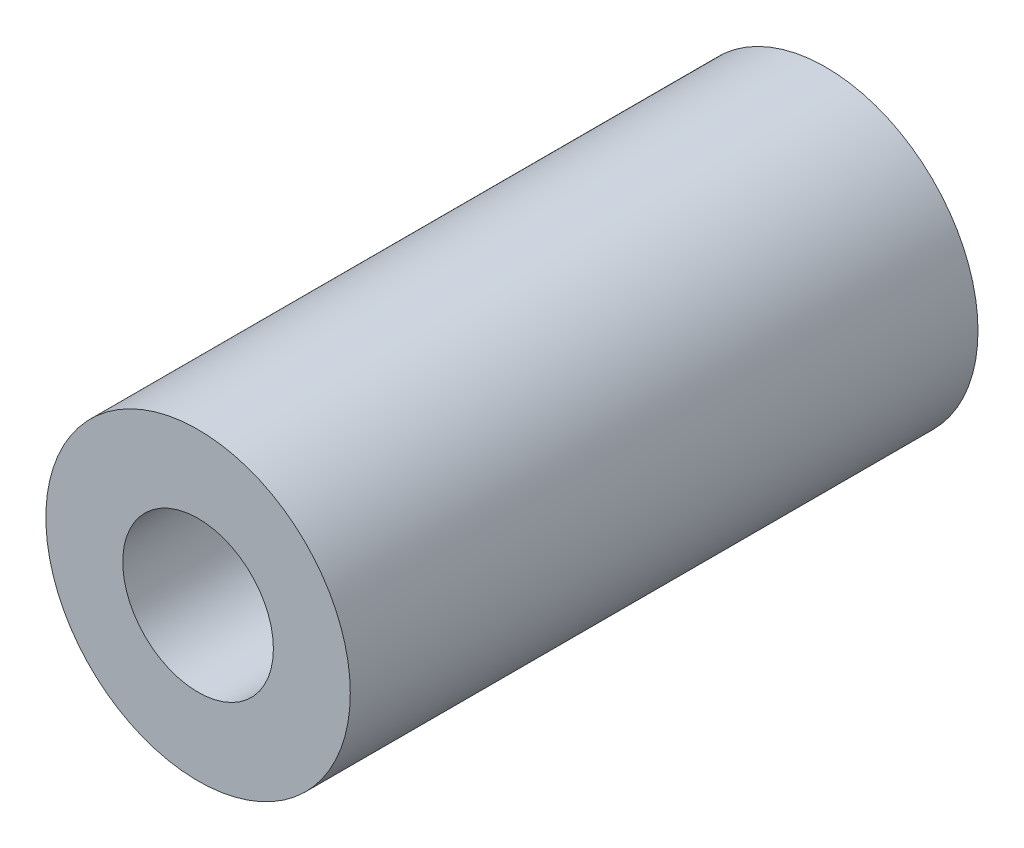
SolidWorks part; units mm, degrees
material "NEOPRENE"
ref_plane "Front Plane" through (0, 0, 0) normal (0, 0, 1) x (1, 0, 0)
ref_plane "Top Plane" through (0, 0, 0) normal (0, 1, 0) x (1, 0, 0)
ref_plane "Right Plane" through (0, 0, 0) normal (1, 0, 0) x (0, 0, -1)
sketch "Sketch1" plane through (0, 0, 0) normal (0, 0, 1) x (1, 0, 0)
  circle A0 centre (0, 0) radius 4.85
  circle A1 centre (0, 0) radius 2.4
  dimension "D1" = 9.7
  dimension "D2" = 4.8
extrude "Boss-Extrude1" add sketch "Sketch1" along normal blind 20
